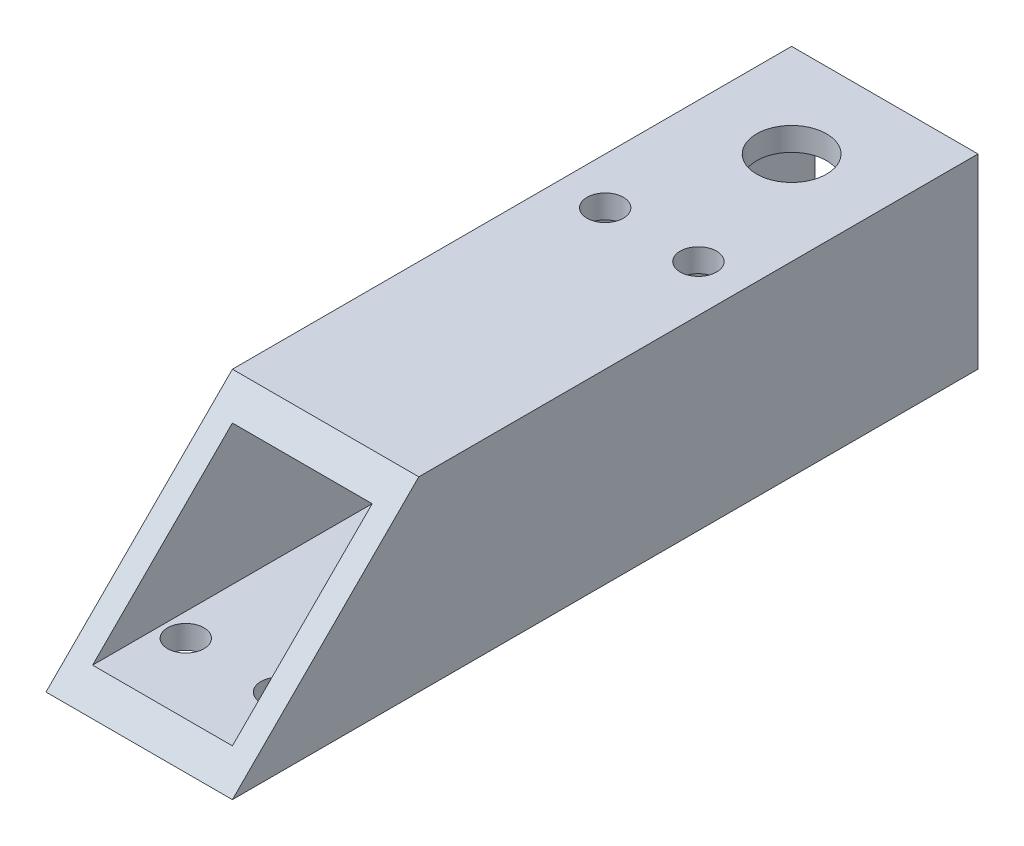
SolidWorks part; units mm, degrees
ref_plane "Front Plane" through (0, 0, 0) normal (0, 0, 1) x (1, 0, 0)
ref_plane "Top Plane" through (0, 0, 0) normal (0, 1, 0) x (1, 0, 0)
ref_plane "Right Plane" through (0, 0, 0) normal (1, 0, 0) x (0, 0, -1)
sketch "Sketch1" plane through (0, 0, 0) normal (0, 0, 1) x (1, 0, 0)
  line L1 (-12.7, -12.7) -> (12.7, -12.7)
  line L2 (-12.7, -12.7) -> (-12.7, 12.7)
  line L3 (-12.7, 12.7) -> (12.7, 12.7)
  line L4 (12.7, -12.7) -> (12.7, 12.7)
  line L5 (-12.7, -12.7) -> (12.7, 12.7) construction
  line L6 (-12.7, 12.7) -> (12.7, -12.7) construction
  point P0 (0, 0)
  dimension "D1" = 25.4
  dimension "D2" = 25.4
extrude "Boss-Extrude1" add sketch "Sketch1" along normal blind 101.6 contours L2 L1 L4 L3
sketch "Sketch2" plane through (0, 0, 101.6) normal (0, 0, 1) x (1, 0, 0)
  line L1 (-9.525, -9.525) -> (9.525, -9.525)
  line L2 (-9.525, -9.525) -> (-9.525, 9.525)
  line L3 (-9.525, 9.525) -> (9.525, 9.525)
  line L4 (9.525, -9.525) -> (9.525, 9.525)
  line L5 (-9.525, -9.525) -> (9.525, 9.525) construction
  line L6 (-9.525, 9.525) -> (9.525, -9.525) construction
  point P0 (0, 0)
  dimension "D1" = 19.05
  dimension "D2" = 19.05
extrude "Cut-Extrude1" cut sketch "Sketch2" against normal through all
sketch "Sketch4" plane through (12.7, 0, 0) normal (1, 0, 0) x (0, 0, -1)
  line L0 (-101.6, 12.7) -> (-76.2, 12.7)
  line L1 (-101.6, 12.7) -> (0, 12.7) construction
  line L2 (-76.2, 12.7) -> (-101.6, -12.7)
  line L3 (-101.6, -12.7) -> (-101.6, 12.7)
  dimension "D1" = 25.4
extrude "Cut-Extrude2" cut sketch "Sketch4" against normal through all
sketch "Sketch5" plane through (0, -12.7, 0) normal (0, -1, 0) x (1, 0, 0)
  line L0 (-12.7, 101.6) -> (12.7, 101.6) construction
  line L1 (-12.7, 101.6) -> (-12.7, 0) construction
  line L3 (0, 101.6) -> (0, 73.3565) construction
  circle A0 centre (-6.35, 88.9) radius 2.4765
  circle A1 centre (6.35, 88.9) radius 2.4765
  dimension "D1" = 4.953
  dimension "D2" = 12.7
  dimension "D3" = 6.35
extrude "Cut-Extrude3" cut sketch "Sketch5" against normal through all
sketch "Sketch7" plane through (0, 12.7, 0) normal (0, 1, 0) x (1, 0, 0)
  line L0 (-12.7, 0) -> (12.7, 0) construction
  line L1 (-12.7, -76.2) -> (-12.7, 0) construction
  circle A0 centre (0, -12.7) radius 4.7625
  dimension "D1" = 9.525
  dimension "D2" = 12.7
  dimension "D3" = 12.7
extrude "Cut-Extrude5" cut sketch "Sketch7" against normal through all
sketch "Sketch8" plane through (0, -12.7, 0) normal (0, -1, 0) x (1, 0, 0)
  line L0 (-12.7, 0) -> (12.7, 0) construction
  line L1 (12.7, 101.6) -> (12.7, 0) construction
  circle A2 centre (6.35, 31.75) radius 2.4765
  circle A3 centre (-6.35, 31.75) radius 2.4765
  point P8 (0, 0)
  dimension "D4" = 4.953
  dimension "D1" = 31.75
  dimension "D2" = 6.35
  dimension "D3" = 12.7
extrude "Cut-Extrude6" cut sketch "Sketch8" against normal through all
